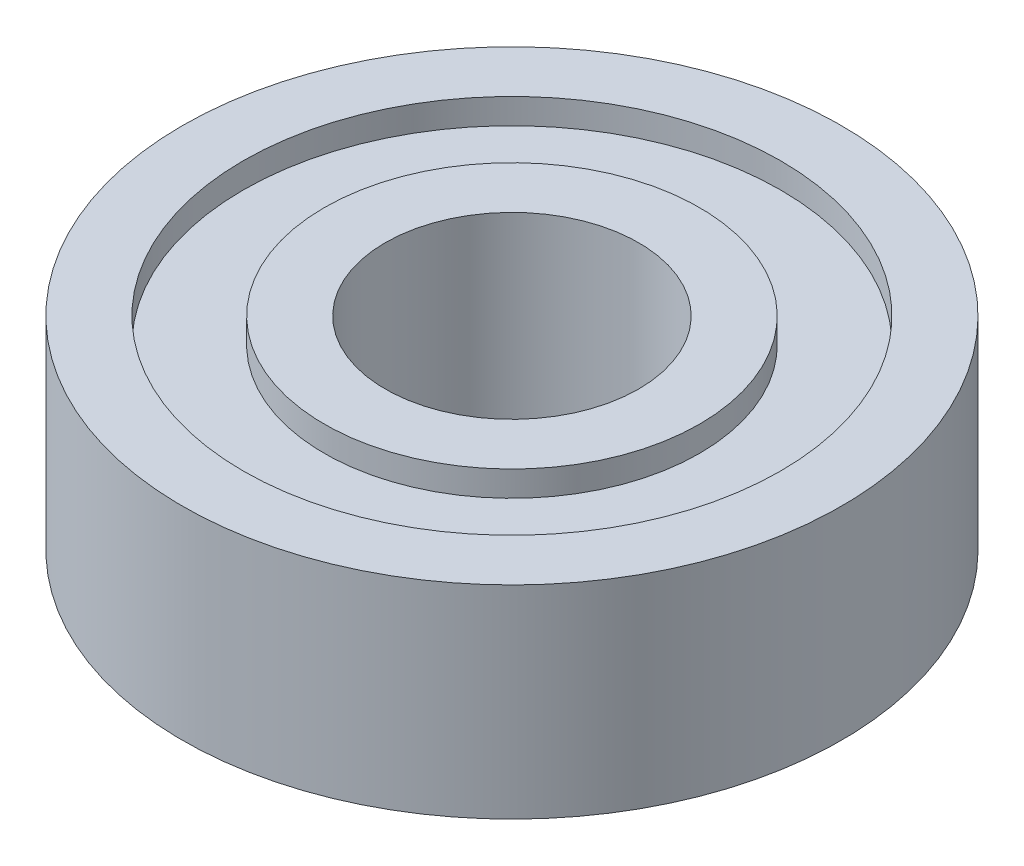
SolidWorks part; units mm, degrees
ref_plane "Alzado" through (0, 0, 0) normal (0, 0, 1) x (1, 0, 0)
ref_plane "Planta" through (0, 0, 0) normal (0, 1, 0) x (1, 0, 0)
ref_plane "Vista lateral" through (0, 0, 0) normal (1, 0, 0) x (0, 0, -1)
sketch "Croquis1" plane through (0, 0, 0) normal (0, 0, 1) x (1, 0, 0)
  line L0 (0, 40.4737) -> (0, -33.1507) construction
  line L1 (-6.5, 0) -> (-2.5, 0) construction
  line L2 (-6.5, 2) -> (-5.3, 2)
  line L3 (-6.5, 2) -> (-6.5, -2)
  line L4 (-6.5, -2) -> (-5.3, -2)
  line L5 (-2.5, 2) -> (-2.5, -2)
  line L6 (-5.3, -2) -> (-5.3, -1.5)
  line L7 (-5.3, -1.5) -> (-3.7, -1.5)
  line L8 (-3.7, -1.5) -> (-3.7, -2)
  line L9 (-3.7, 1.5) -> (-3.7, 2)
  line L10 (-5.3, 1.5) -> (-3.7, 1.5)
  line L11 (-5.3, 2) -> (-5.3, 1.5)
  line L12 (-3.7, 2) -> (-2.5, 2)
  line L13 (-3.7, -2) -> (-2.5, -2)
  point P11 (-4.5, -1.5)
  point P14 (-4.5, 0)
  dimension "D1" = 5
  dimension "D2" = 13
  dimension "D3" = 1.2
  dimension "D4" = 4
  dimension "D5" = 3
revolve "Revolución1" add sketch "Croquis1" angle 360 about L0
equation "\"D5@Croquis1\"=\"D4@Croquis1\"-1"
